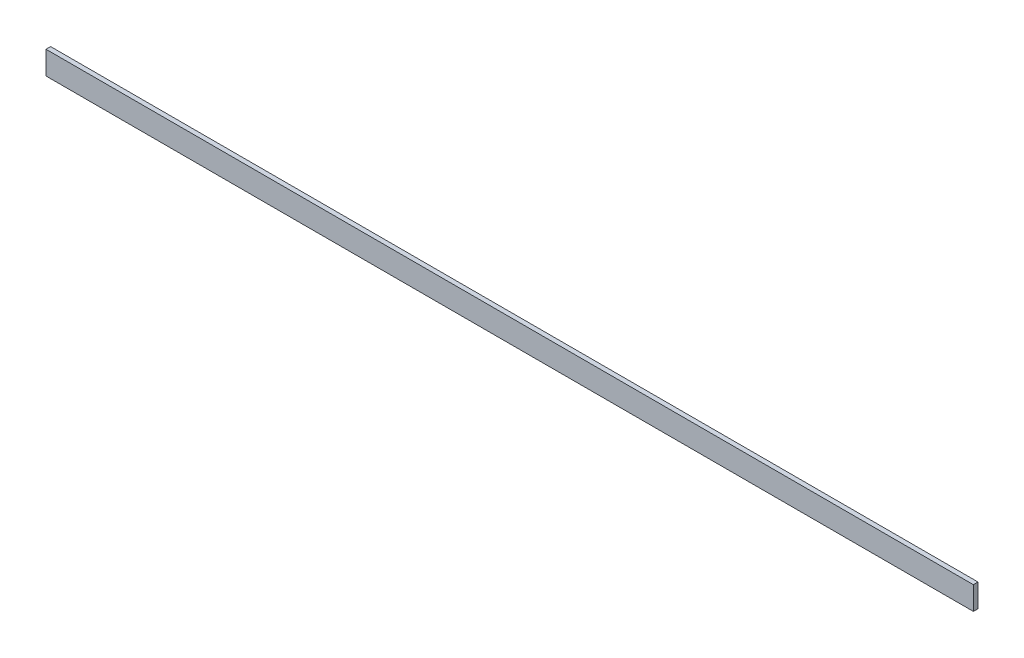
SolidWorks part; units mm, degrees
material "PMMA"
ref_plane "Front Plane" through (0, 0, 0) normal (0, 0, 1) x (1, 0, 0)
ref_plane "Top Plane" through (0, 0, 0) normal (0, 1, 0) x (1, 0, 0)
ref_plane "Right Plane" through (0, 0, 0) normal (1, 0, 0) x (0, 0, -1)
sketch "Sketch2" plane through (0, 0, 0) normal (0, 0, 1) x (1, 0, 0)
  line L1 (0, 0) -> (600, 0)
  line L2 (0, 0) -> (0, 15)
  line L3 (0, 15) -> (600, 15)
  line L4 (600, 0) -> (600, 15)
  dimension "D1" = 600
  dimension "D2" = 15
extrude "Boss-Extrude1" add sketch "Sketch2" along normal blind 3
